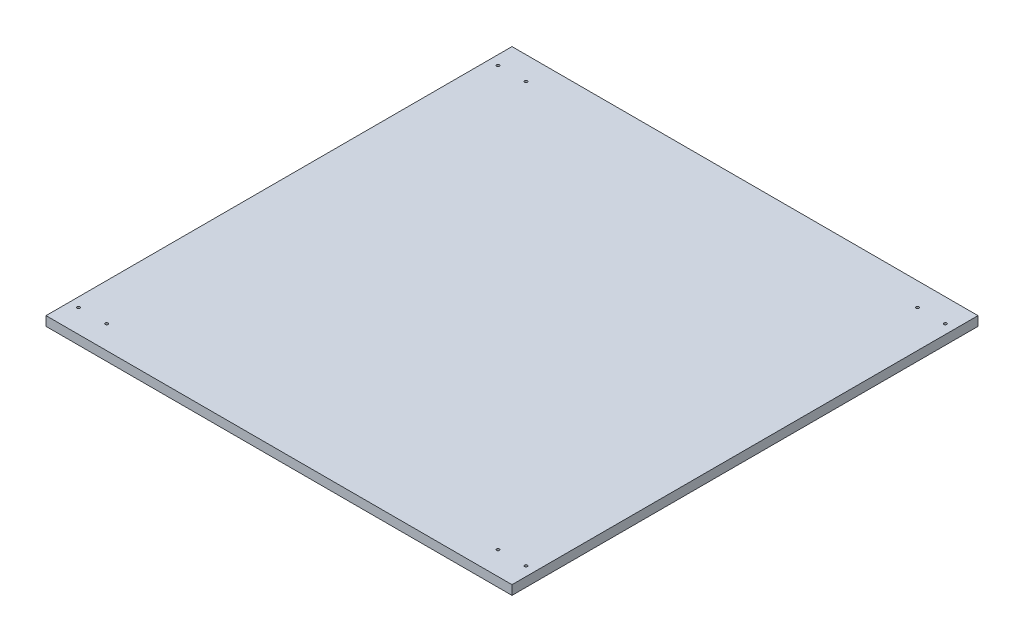
SolidWorks part; units mm, degrees
ref_plane "Front Plane" through (0, 0, 0) normal (0, 0, 1) x (1, 0, 0)
ref_plane "Top Plane" through (0, 0, 0) normal (0, 1, 0) x (1, 0, 0)
ref_plane "Right Plane" through (0, 0, 0) normal (1, 0, 0) x (0, 0, -1)
sketch "Sketch1" plane through (0, 0, 0) normal (0, 1, 0) x (1, 0, 0)
  line L0 (0, 0) -> (500, 0)
  line L1 (500, 0) -> (500, 500)
  line L2 (500, 500) -> (0, 500)
  line L3 (0, 500) -> (0, 0)
  dimension "D1" = 500
  dimension "D2" = 500
  dimension "D3" = 500
extrude "Boss-Extrude1" add sketch "Sketch1" along normal blind 10
sketch "Sketch2" plane through (0, 10, 0) normal (0, 1, 0) x (1, 0, 0)
  line L0 (0, 0) -> (500, 0) construction
  line L1 (0, 500) -> (0, 0) construction
  line L2 (500, 0) -> (500, 500) construction
  line L3 (500, 500) -> (0, 500) construction
  circle A0 centre (10, 25) radius 1.5
  circle A1 centre (10, 475) radius 1.5
  circle A2 centre (40, 475) radius 1.5
  circle A3 centre (40, 25) radius 1.5
  circle A4 centre (460, 475) radius 1.5
  circle A5 centre (490, 475) radius 1.5
  circle A6 centre (460, 25) radius 1.5
  circle A7 centre (490, 25) radius 1.5
  dimension "D3" = 3
  dimension "D7" = 3
  dimension "D9" = 3
  dimension "D10" = 3
  dimension "D13" = 25
  dimension "D18" = 3
  dimension "D19" = 3
  dimension "D23" = 3
  dimension "D24" = 3
  dimension "D1" = 450
  dimension "D2" = 25
  dimension "D4" = 10
  dimension "D5" = 30
  dimension "D6" = 25
  dimension "D8" = 10
  dimension "D11" = 30
  dimension "D12" = 25
  dimension "D14" = 10
  dimension "D15" = 25
  dimension "D16" = 25
  dimension "D17" = 30
  dimension "D20" = 10
  dimension "D21" = 25
  dimension "D22" = 30
extrude "Cut-Extrude1" cut sketch "Sketch2" against normal blind 10
